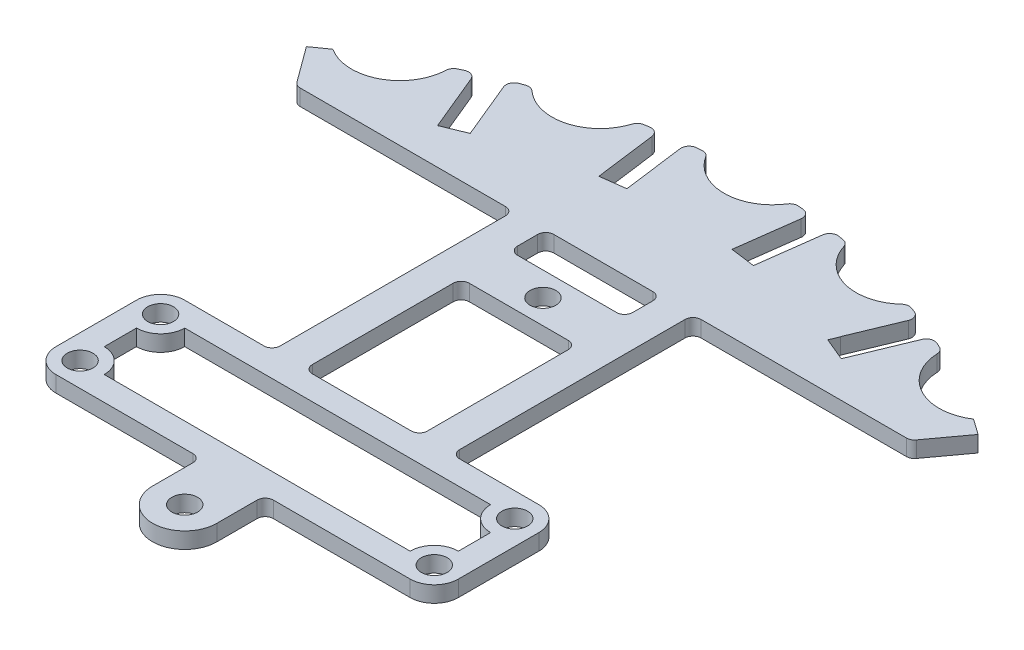
SolidWorks part; units mm, degrees
ref_plane "Front Plane" through (0, 0, 0) normal (0, 0, 1) x (1, 0, 0)
ref_plane "Top Plane" through (0, 0, 0) normal (0, 1, 0) x (1, 0, 0)
ref_plane "Right Plane" through (0, 0, 0) normal (1, 0, 0) x (0, 0, -1)
sketch "Sketch1" plane through (0, 0, 0) normal (0, 1, 0) x (1, 0, 0)
  line L0 (-16.15, 22) -> (-11.15, 22)
  line L1 (22, 22) -> (16.15, 22)
  line L2 (-4, 0) -> (-4, 6)
  line L3 (-22, 6) -> (-4, 6)
  line L4 (-25, 9) -> (-25, 19)
  line L5 (-11.15, 22) -> (-11.15, 52)
  line L6 (-11.15, 52) -> (-38.1728, 52)
  line L8 (22, 6) -> (4, 6)
  line L9 (4, 0) -> (4, 6)
  line L10 (25, 9) -> (25, 19)
  line L11 (16.15, 22) -> (11.15, 22)
  line L12 (11.15, 52) -> (38.1728, 52)
  line L13 (26.496, 68.0212) -> (26.4715, 68.0313)
  line L14 (11.15, 22) -> (11.15, 52)
  line L15 (24.0921, 58.1933) -> (25.5379, 57.5947)
  line L16 (24.0921, 58.1933) -> (22.6463, 58.7918)
  line L17 (26.4715, 68.0313) -> (22.6463, 58.7918)
  line L18 (29.363, 66.8342) -> (25.5379, 57.5947)
  line L20 (11.0645, 72.1566) -> (9.7593, 62.2422)
  line L21 (7.988, 72.5616) -> (6.6827, 62.6472)
  line L22 (6.6827, 62.6472) -> (9.7593, 62.2422)
  line L23 (-26.4961, 68.0217) -> (-22.6693, 58.7829)
  line L24 (-22.6693, 58.7829) -> (-24.1027, 58.1892)
  line L25 (-29.363, 66.8342) -> (-25.5362, 57.5954)
  line L26 (-25.5362, 57.5954) -> (-24.1027, 58.1892)
  line L28 (-16.15, 22) -> (-22, 22)
  line L29 (-7.988, 72.5616) -> (-6.6827, 62.6472)
  line L30 (-6.6827, 62.6472) -> (-8.221, 62.4447)
  line L31 (-11.0645, 72.1566) -> (-9.7593, 62.2422)
  line L32 (-9.7593, 62.2422) -> (-8.221, 62.4447)
  line L33 (38.1728, 52) -> (43.1986, 58.8462)
  line L34 (-38.1728, 52) -> (-43.1986, 58.8462)
  arc A0 (-22, 6) -> (-25, 9) centre (-22, 9) cw
  arc A1 (-25, 19) -> (-22, 22) centre (-22, 19) cw
  arc A2 (-4.9971, 72.8288) -> (4.9971, 72.8288) centre (0, 73) ccw
  arc A3 (-7.988, 72.5616) -> (-7.8293, 71.356) centre (0, 73) ccw
  arc A4 (14.0227, 71.6405) -> (23.6763, 69.0539) centre (18.8938, 70.5126) ccw
  arc A5 (43.1986, 58.8462) -> (40.742, 60.573) centre (0, 0) ccw
  arc A6 (26.4961, 68.0217) -> (23.6763, 69.0539) centre (0, 0) ccw
  circle A7 centre (0, 0) radius 1.6
  arc A8 (-4, 0) -> (4, 0) centre (0, 0) ccw
  arc A9 (25, 19) -> (22, 22) centre (22, 19) ccw
  arc A10 (22, 6) -> (25, 9) centre (22, 9) ccw
  arc A11 (7.988, 72.5616) -> (4.9971, 72.8288) centre (0, 0) ccw
  arc A12 (11.0645, 72.1566) -> (10.9058, 70.9509) centre (18.8938, 70.5126) ccw
  arc A13 (32.0868, 65.5701) -> (40.742, 60.573) centre (36.5, 63.2199) ccw
  arc A14 (29.363, 66.8342) -> (28.8968, 65.708) centre (36.5, 63.2199) ccw
  arc A15 (-32.0868, 65.5701) -> (-40.742, 60.573) centre (-36.5, 63.2199) cw
  arc A16 (-14.0227, 71.6405) -> (-23.6763, 69.0539) centre (-18.8938, 70.5126) cw
  arc A17 (-11.0645, 72.1566) -> (-10.9058, 70.9509) centre (-18.8938, 70.5126) cw
  arc A18 (-29.363, 66.8342) -> (-28.8977, 65.7107) centre (-36.5, 63.2199) cw
  arc A19 (-11.0645, 72.1566) -> (-14.0227, 71.6405) centre (0, 0) ccw
  arc A20 (-23.6763, 69.0539) -> (-26.4961, 68.0217) centre (0, 0) ccw
  arc A21 (-40.742, 60.573) -> (-43.1986, 58.8462) centre (0, 0) ccw
  arc A22 (-4.9971, 72.8288) -> (-7.988, 72.5616) centre (0, 0) ccw
  arc A23 (14.0227, 71.6405) -> (11.0645, 72.1566) centre (0, 0) ccw
  arc A24 (32.0868, 65.5701) -> (29.363, 66.8342) centre (0, 0) ccw
  arc A25 (-29.363, 66.8342) -> (-32.0868, 65.5701) centre (0, 0) ccw
  arc A26 (7.8293, 71.356) -> (7.988, 72.5616) centre (0, 73) ccw
  arc A27 (25.8999, 66.6506) -> (26.4961, 68.0217) centre (18.8938, 70.5126) ccw
  arc A29 (-26.0308, 66.8982) -> (-26.4961, 68.0217) centre (-18.8938, 70.5126) cw
  point P12 (0, 22)
extrude "Boss-Extrude1" add sketch "Sketch1" along normal blind 2 contours L25 A25 A15 A21 L34 L6 L5 L0 L28 A1 L4 A0 L3 L2 A8 L9 L8 A10 L10 A9 L1 L11 L14 L12 L33 A5 A13 A24 L18 L15 L16 L17 A6 A4 A23 L20 L22 L21 A11 A2 A22 L29 L30 L32 L31
sketch "Sketch2" plane through (0, 2, 0) normal (0, 1, 0) x (1, 0, 0)
  circle A0 centre (0, 73) radius 6
  circle A1 centre (-18.8938, 70.5126) radius 6
  circle A2 centre (-36.5, 63.2199) radius 6
  circle A3 centre (18.8938, 70.5126) radius 6
  circle A4 centre (36.5, 63.2199) radius 6
extrude "Cut-Extrude1" cut sketch "Sketch2" against normal blind 2
sketch "Sketch4" plane through (0, 2, 0) normal (0, 1, 0) x (1, 0, 0)
  line L0 (-25.5362, 57.5954) -> (-25.077, 56.4868)
  line L1 (-25.5362, 57.5954) -> (-22.6693, 58.7829)
  line L2 (-22.6693, 58.7829) -> (-22.2101, 57.6743)
  line L3 (-22.2101, 57.6743) -> (-25.077, 56.4868)
  line L4 (-9.7593, 62.2422) -> (-9.6026, 61.0524)
  line L5 (-6.6827, 62.6472) -> (-6.5261, 61.4575)
  line L6 (-6.5261, 61.4575) -> (-9.6026, 61.0524)
  line L7 (-9.7593, 62.2422) -> (-6.6827, 62.6472)
  line L9 (9.7593, 62.2422) -> (6.6827, 62.6472)
  line L10 (6.5261, 61.4575) -> (9.6026, 61.0524)
  line L11 (6.6827, 62.6472) -> (6.5261, 61.4575)
  line L12 (9.7593, 62.2422) -> (9.6026, 61.0524)
  line L13 (22.2101, 57.6743) -> (25.077, 56.4868)
  line L14 (22.6693, 58.7829) -> (22.2101, 57.6743)
  line L15 (25.5362, 57.5954) -> (22.6693, 58.7829)
  line L16 (25.5362, 57.5954) -> (25.077, 56.4868)
  circle A0 centre (0, 0) radius 70.5
  circle A1 centre (0, 0) radius 106.1641
  arc M1 (-13.0393, 71.826) -> (-24.6206, 68.7228) centre (-18.8938, 70.5126) cw
  arc M2 (-24.6206, 68.7228) -> (-26.4961, 68.0217) centre (0, 0) ccw
  line M3 (-26.4961, 68.0217) -> (-22.6693, 58.7829)
  line M4 (-22.6693, 58.7829) -> (-25.5362, 57.5954)
  line M5 (-25.5362, 57.5954) -> (-29.363, 66.8342)
  arc M6 (-29.363, 66.8342) -> (-31.1849, 66.0038) centre (0, 0) ccw
  arc M7 (-31.1849, 66.0038) -> (-41.5685, 60.0088) centre (-36.5, 63.2199) cw
  arc M8 (-41.5685, 60.0088) -> (-43.1986, 58.8462) centre (0, 0) ccw
  line M9 (-43.1986, 58.8462) -> (-38.1728, 52)
  line M27 (38.1728, 52) -> (43.1986, 58.8462)
  arc M28 (43.1986, 58.8462) -> (41.5685, 60.0088) centre (0, 0) ccw
  arc M29 (41.5685, 60.0088) -> (31.1849, 66.0038) centre (36.5, 63.2199) cw
  arc M30 (31.1849, 66.0038) -> (29.363, 66.8342) centre (0, 0) ccw
  line M31 (29.363, 66.8342) -> (25.5379, 57.5947)
  line M32 (25.5379, 57.5947) -> (22.6463, 58.7918)
  line M33 (22.6463, 58.7918) -> (26.4715, 68.0313)
  arc M34 (26.4715, 68.0313) -> (24.6206, 68.7228) centre (0, 0) ccw
  arc M35 (24.6206, 68.7228) -> (13.0393, 71.826) centre (18.8938, 70.5126) cw
  arc M36 (13.0393, 71.826) -> (11.0645, 72.1566) centre (0, 0) ccw
  line M37 (11.0645, 72.1566) -> (9.7593, 62.2422)
  line M38 (9.7593, 62.2422) -> (6.6827, 62.6472)
  line M39 (6.6827, 62.6472) -> (7.988, 72.5616)
  arc M40 (7.988, 72.5616) -> (5.9949, 72.7534) centre (0, 0) ccw
  arc M41 (5.9949, 72.7534) -> (-5.9949, 72.7534) centre (0, 73) cw
  arc M42 (-5.9949, 72.7534) -> (-7.988, 72.5616) centre (0, 0) ccw
  line M43 (-7.988, 72.5616) -> (-6.6827, 62.6472)
  line M44 (-6.6827, 62.6472) -> (-9.7593, 62.2422)
  line M45 (-9.7593, 62.2422) -> (-11.0645, 72.1566)
  arc M46 (-11.0645, 72.1566) -> (-13.0393, 71.826) centre (0, 0) ccw
extrude "Cut-Extrude3" cut sketch "Sketch4" against normal blind 5 contours A1 A0 M29 M28 M27 M9 M8 M7 M6 M5 M3 M2 M1 M46 M45 M43 M42 M41 M40 M39 M37 M36 M35 M34 M33 M31 M30 | A0 M45 M46 M1 | A0 M1 M2 M3 | A0 M5 M6 M7 | A0 M7 M8 M9 | A0 M41 M42 M43 | A0 M39 M40 M41 | L12 L11 L10 M38 | L6 L5 L4 M44 | L3 L2 L0 M4 | A0 M35 M36 M37 | A0 M33 M34 M35 | A0 M29 M30 M31 | A0 M27 M28 M29 | L16 L14 L13 M32
sketch "Sketch5" plane through (0, 2, 0) normal (0, 1, 0) x (1, 0, 0)
  line L0 (-22, 16) -> (-22, 12)
  line L2 (-19, 19) -> (19, 19)
  line L4 (22, 16) -> (22, 12)
  line L6 (-19, 9) -> (19, 9)
  line L7 (7.15, 52) -> (7.15, 22)
  line L8 (7.15, 22) -> (-7.15, 22)
  line L9 (-7.15, 22) -> (-7.15, 52)
  line L10 (-7.15, 52) -> (7.15, 52)
  circle A0 centre (22, 19) radius 1.6
  circle A1 centre (-22, 19) radius 1.6
  circle A2 centre (-22, 9) radius 1.6
  circle A3 centre (22, 9) radius 1.6
  arc A4 (-22, 16) -> (-19, 19) centre (-22, 19) ccw
  arc A5 (-19, 9) -> (-22, 12) centre (-22, 9) ccw
  arc A6 (22, 12) -> (19, 9) centre (22, 9) ccw
  arc A7 (19, 19) -> (22, 16) centre (22, 19) ccw
extrude "Cut-Extrude4" cut sketch "Sketch5" against normal blind 5
sketch "Sketch6" plane through (0, 2, 0) normal (0, 1, 0) x (1, 0, 0)
  line L1 (0, 44) -> (-7.15, 44)
  line L2 (-7.15, 52) -> (-7.15, 22) construction
  line L3 (-7.15, 44) -> (-7.15, 36)
  line L4 (-7.15, 36) -> (7.15, 36)
  line L5 (7.15, 22) -> (7.15, 52) construction
  line L6 (7.15, 36) -> (7.15, 44)
  line L7 (7.15, 44) -> (0, 44)
  circle A0 centre (0, 40) radius 1.6
extrude "Boss-Extrude2" add sketch "Sketch6" against normal up to surface (2 mm away) up to face at (22, 0, -7.4)
fillet "Fillet1" radius 1 4 edges at (7.15, 1, -44) (-7.15, 1, -44) (-7.15, 1, -36) (7.15, 1, -36)
fillet "Fillet2" radius 1 4 edges at (-7.15, 1, -22) (7.15, 1, -22) (7.15, 1, -52) (-7.15, 1, -52)
fillet "Fillet3" radius 1 2 edges at (-38.1728, 1, -52) (38.1728, 1, -52)
sketch "Sketch7" plane through (0, 2, 0) normal (0, 1, 0) x (1, 0, 0)
  line L0 (-7.15, 48) -> (-7.15, 29)
  line L1 (-7.15, 51) -> (-7.15, 45) construction
  line L2 (-7.15, 35) -> (-7.15, 23) construction
  line L3 (-7.15, 29) -> (7.15, 29)
  line L4 (7.15, 23) -> (7.15, 35) construction
  line L5 (7.15, 29) -> (7.15, 48)
  line L6 (7.15, 45) -> (7.15, 51) construction
  line L7 (7.15, 48) -> (-7.15, 48)
extrude "Cut-Extrude5" cut sketch "Sketch7" against normal blind 10
sketch "Sketch8" plane through (0, 2, 0) normal (0, 1, 0) x (1, 0, 0)
  line L0 (7.15, 47.5) -> (7.15, 41.5)
  line L2 (0, 47.5) -> (7.15, 47.5)
  line L3 (7.15, 23) -> (7.15, 51) construction
  line L7 (-7.15, 51) -> (-7.15, 23) construction
  line L9 (-7.15, 47.5) -> (0, 47.5)
  line L10 (7.15, 41.5) -> (-7.15, 41.5)
  line L11 (-7.15, 41.5) -> (-7.15, 47.5)
  circle A0 centre (0, 44.5) radius 1.6
extrude "Boss-Extrude3" add sketch "Sketch8" against normal up to surface (2 mm away) up to face at (0, 0, -37)
fillet "Fillet4" radius 1 10 edges at (-4, 1, -6) (4, 1, -6) (11.15, 1, -22) (-11.15, 1, -22) (-11.15, 1, -52) (11.15, 1, -52) (-7.15, 1, -41.5) (7.15, 1, -41.5) (7.15, 1, -47.5) (-7.15, 1, -47.5)
fillet "Fillet5" radius 1 16 edges at (30.5094, 1, -63.5565) (28.4065, 1, -64.5238) (10.7381, 1, -69.6774) (23.3678, 1, -66.5146) (13.0202, 1, -69.2873) (25.515, 1, -65.7209) (7.6616, 1, -70.0825) (5.3563, 1, -70.2962) (-5.3563, 1, -70.2962) (-7.6616, 1, -70.0825) (-30.5094, 1, -63.5565) (-28.4061, 1, -64.524) (-25.5392, 1, -65.7115) (-13.0202, 1, -69.2873) (-23.3678, 1, -66.5146) (-10.7381, 1, -69.6774)
